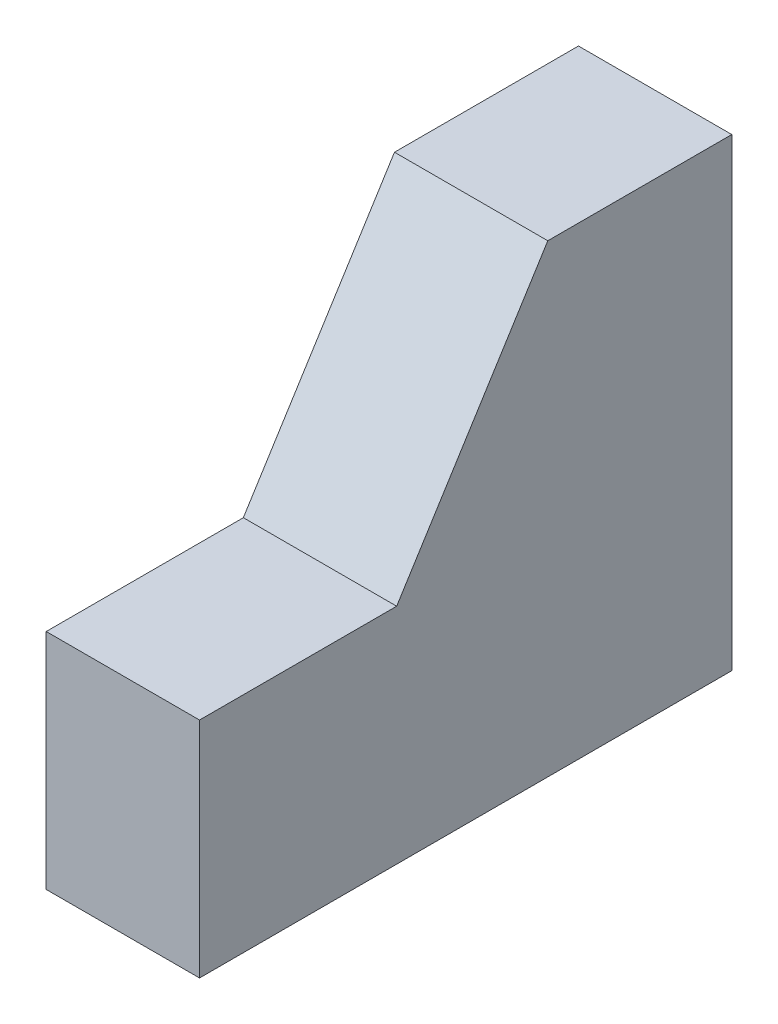
SolidWorks part; units mm, degrees
ref_plane "Front Plane" through (0, 0, 0) normal (0, 0, 1) x (1, 0, 0)
ref_plane "Top Plane" through (0, 0, 0) normal (0, 1, 0) x (1, 0, 0)
ref_plane "Right Plane" through (0, 0, 0) normal (1, 0, 0) x (0, 0, -1)
sketch "Sketch1" plane through (0, 0, 0) normal (1, 0, 0) x (0, 0, -1)
  line L0 (0, 0) -> (0, 10.2)
  line L1 (0, 10.2) -> (9, 10.2)
  line L2 (9, 10.2) -> (15.9, 21.2)
  line L3 (15.9, 21.2) -> (24.3, 21.2)
  line L4 (24.3, 21.2) -> (24.3, 0)
  line L5 (24.3, 0) -> (0, 0)
  dimension "D1" = 8.4
  dimension "D2" = 9
  dimension "D3" = 24.3
  dimension "D4" = 21.2
  dimension "D5" = 10.2
extrude "Boss-Extrude1" add sketch "Sketch1" along normal blind 7
sketch "Sketch2" plane through (0, 0, 0) normal (0, -1, 0) x (1, 0, 0)
  line L0 (3.5, 0) -> (3.5, -24.3) construction
  line L1 (7, 0) -> (0, 0) construction
  line L2 (7, -24.3) -> (0, -24.3) construction
  circle A0 centre (3.5, -5.35) radius 1.45
  circle A1 centre (3.5, -14.75) radius 1.45
  point P10 (0, 0)
  point P11 (0, 0)
  dimension "D1" = 6.5
  dimension "D2" = 2.9
  dimension "D3" = 2.9
  dimension "D4" = 3.9
extrude "Cut-Extrude1" cut sketch "Sketch2" against normal blind 7.5
sketch "Sketch3" plane through (0, 0, -24.3) normal (0, 0, -1) x (-1, 0, 0)
  line L0 (-3.5, 21.2) -> (-3.5, 0) construction
  line L1 (-7, 21.2) -> (0, 21.2) construction
  line L2 (-7, 0) -> (0, 0) construction
  circle A0 centre (-3.5, 15.75) radius 1.45
  circle A1 centre (-3.5, 5.35) radius 1.45
  dimension "D1" = 2.9
  dimension "D2" = 2.9
  dimension "D3" = 7.5
  dimension "D4" = 4
extrude "Cut-Extrude2" cut sketch "Sketch3" against normal blind 7.5
